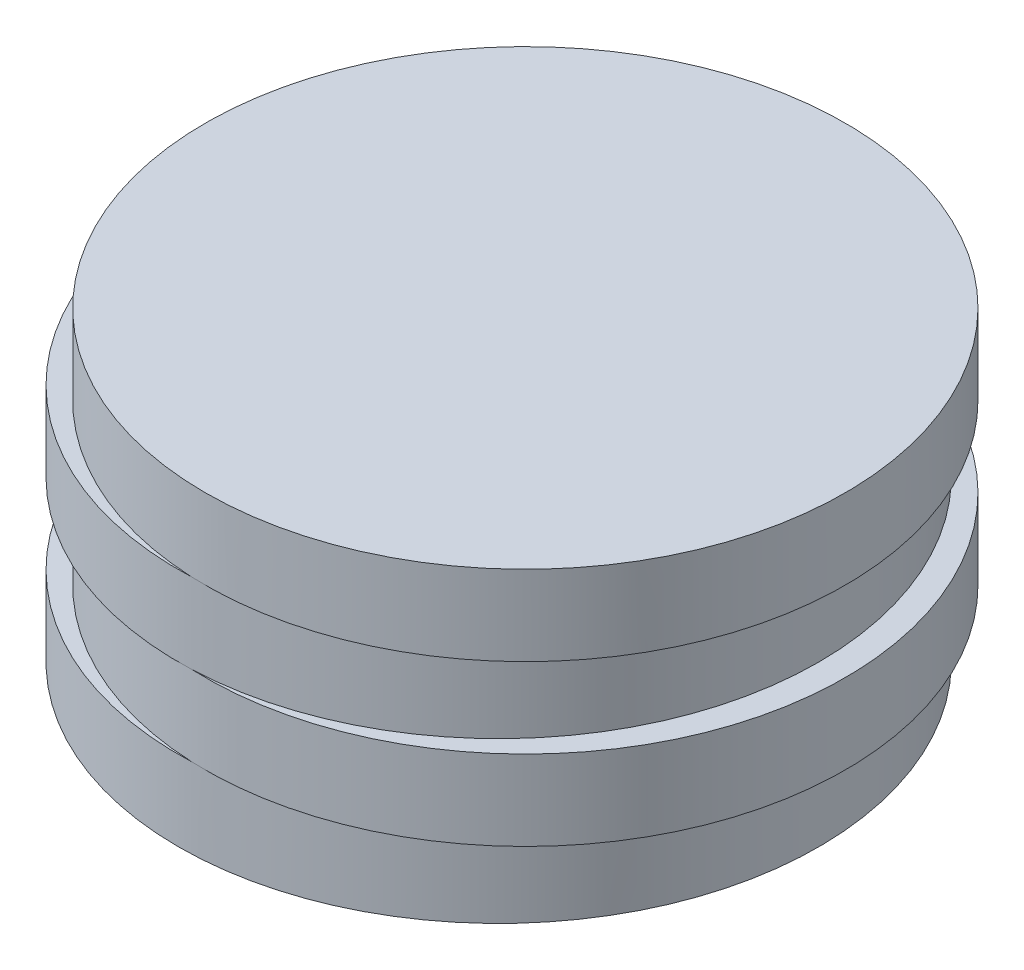
SolidWorks part; units mm, degrees
ref_plane "Front Plane" through (0, 0, 0) normal (0, 0, 1) x (1, 0, 0)
ref_plane "Top Plane" through (0, 0, 0) normal (0, 1, 0) x (1, 0, 0)
ref_plane "Right Plane" through (0, 0, 0) normal (1, 0, 0) x (0, 0, -1)
sketch "Sketch1" plane through (0, 0, 0) normal (0, 1, 0) x (1, 0, 0)
  circle A0 centre (0, 0) radius 36
extrude "Boss-Extrude1" add sketch "Sketch1" along normal blind 9
sketch "Sketch2" plane through (0, 9, 0) normal (0, 1, 0) x (1, 0, 0)
  line L0 (0, 0) -> (3, 0)
  circle A0 centre (3, 0) radius 36
extrude "Boss-Extrude2" add sketch "Sketch2" along normal blind 9
sketch "Sketch3" plane through (0, 18, 0) normal (0, 1, 0) x (1, 0, 0)
  circle A0 centre (0, 0) radius 36
extrude "Boss-Extrude3" add sketch "Sketch3" along normal blind 9
sketch "Sketch4" plane through (0, 27, 0) normal (0, 1, 0) x (1, 0, 0)
  line L0 (0, 0) -> (3, 0)
  circle A0 centre (3, 0) radius 36
extrude "Boss-Extrude4" add sketch "Sketch4" along normal blind 9
